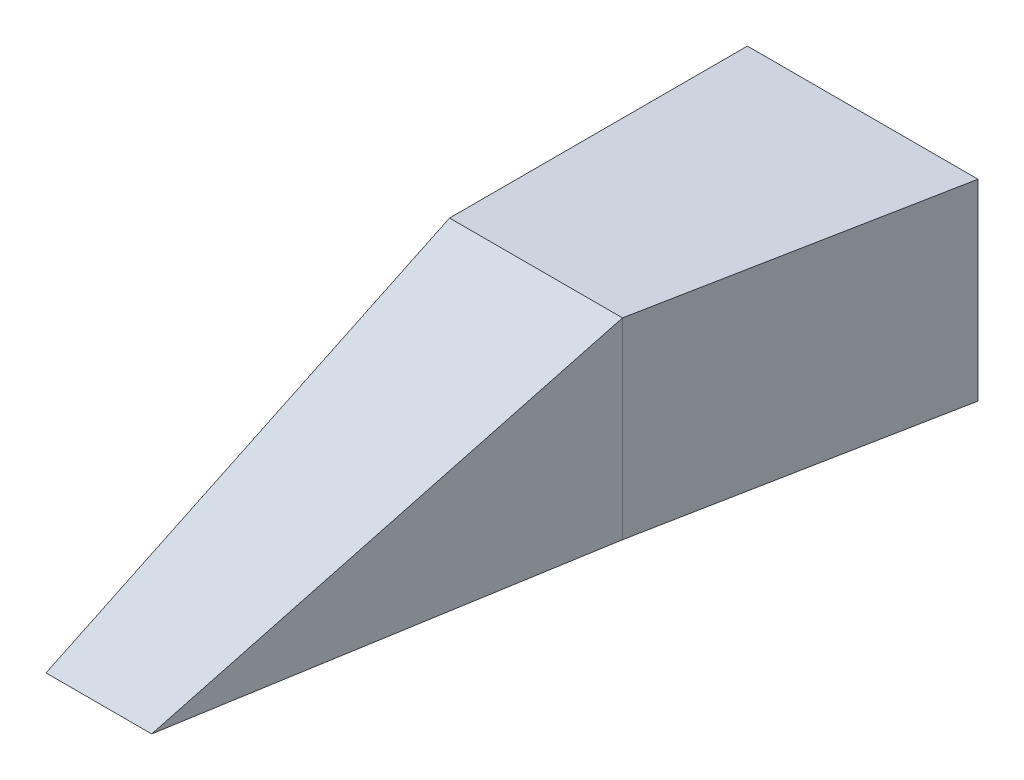
SolidWorks part; units mm, degrees
ref_plane "Front Plane" through (0, 0, 0) normal (0, 0, 1) x (1, 0, 0)
ref_plane "Top Plane" through (0, 0, 0) normal (0, 1, 0) x (1, 0, 0)
ref_plane "Right Plane" through (0, 0, 0) normal (1, 0, 0) x (0, 0, -1)
sketch "Sketch1" plane through (0, 0, 0) normal (0, 1, 0) x (1, 0, 0)
  line L0 (0, 1066.8) -> (0, 0)
  line L1 (0, 0) -> (279.4, 0)
  line L2 (279.4, 0) -> (457.2, 1066.8)
  line L3 (457.2, 1066.8) -> (0, 1066.8)
  dimension "D1" = 279.4
  dimension "D2" = 457.2
  dimension "D3" = 1066.8
extrude "Boss-Extrude1" add sketch "Sketch1" along normal blind 508
sketch "Sketch2" plane through (0, 0, 0) normal (-1, 0, 0) x (0, 0, 1)
  line L0 (0, 0) -> (-1066.8, 508)
  line L1 (-1066.8, 508) -> (-1066.8, 732.6724)
  line L2 (-1066.8, 732.6724) -> (0, 732.6724)
  line L3 (0, 732.6724) -> (0, 0)
extrude "Cut-Extrude1" cut sketch "Sketch2" against normal blind 508
sketch "Sketch3" plane through (0, 0, 0) normal (0, -1, 0) x (1, 0, 0)
  line L0 (0, -1066.8) -> (0, -1854.2)
  line L1 (0, -1854.2) -> (609.6, -1854.2)
  line L2 (609.6, -1854.2) -> (457.2, -1066.8)
  line L3 (457.2, -1066.8) -> (0, -1066.8)
  dimension "D1" = 787.4
  dimension "D2" = 609.6
extrude "Boss-Extrude2" add sketch "Sketch3" against normal blind 508
